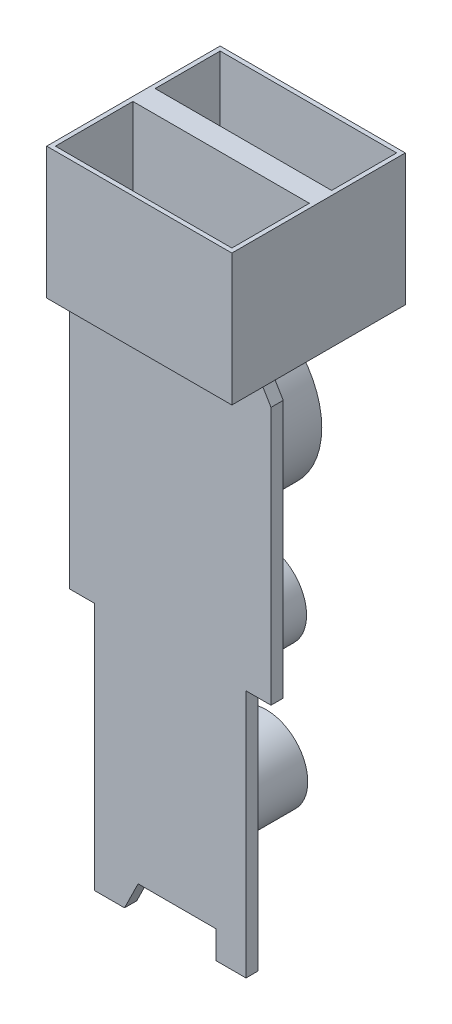
SolidWorks part; units mm, degrees
ref_plane "Front Plane" through (0, 0, 0) normal (0, 0, 1) x (1, 0, 0)
ref_plane "Top Plane" through (0, 0, 0) normal (0, 1, 0) x (1, 0, 0)
ref_plane "Right Plane" through (0, 0, 0) normal (1, 0, 0) x (0, 0, -1)
sketch "Sketch1" plane through (0, 0, 0) normal (0, 1, 0) x (1, 0, 0)
  line L10 (-7.035, 6.59) -> (7.035, 6.59)
  line L11 (-7.035, 6.59) -> (-7.035, -6.59)
  line L12 (-7.035, -6.59) -> (7.035, -6.59)
  line L13 (7.035, 6.59) -> (7.035, -6.59)
  point P0 (0, 0)
  point P5 (0, 0)
  point P6 (0, 0)
  dimension "D1" = 13.18
  dimension "D2" = 14.07
extrude "Boss-Extrude1" add sketch "Sketch1" along normal mid plane 10
sketch "Sketch2" plane through (0, 5, 0) normal (0, 1, 0) x (1, 0, 0)
  line L0 (7.035, 6.59) -> (-7.035, 6.59) construction
  line L1 (-6.705, 6.26) -> (6.705, 6.26)
  line L2 (-6.705, 6.26) -> (-6.705, 1.32)
  line L3 (-6.705, 1.32) -> (6.705, 1.32)
  line L4 (6.705, 6.26) -> (6.705, 1.32)
  line L5 (-7.035, 6.59) -> (-7.035, -6.59) construction
  line L6 (7.035, -6.59) -> (7.035, 6.59) construction
  line L11 (-7.035, -6.59) -> (7.035, -6.59) construction
  line L12 (-6.705, -0.3713) -> (6.705, -0.3713)
  line L13 (-6.705, -0.3713) -> (-6.705, -6.26)
  line L14 (-6.705, -6.26) -> (6.705, -6.26)
  line L15 (6.705, -0.3713) -> (6.705, -6.26)
  dimension "D1" = 0.33
  dimension "D2" = 0.33
  dimension "D3" = 0.33
  dimension "D4" = 0.33
  dimension "D5" = 1.6913
  dimension "D6" = 4.94
extrude "Cut-Extrude1" cut sketch "Sketch2" against normal blind 9
sketch "Sketch3" plane through (0, 0, 0) normal (0, 0, 1) x (1, 0, 0)
  line L0 (7.035, -5) -> (7.65, -6.0304)
  line L1 (7.65, -6.0304) -> (7.65, -25.6304)
  line L2 (7.65, -25.6304) -> (5.75, -25.6304)
  line L3 (5.75, -25.6304) -> (5.75, -44.5304)
  line L4 (5.75, -44.5304) -> (3.48, -44.5304)
  line L5 (3.48, -44.5304) -> (3.48, -42.4304)
  line L6 (3.48, -42.4304) -> (-2.449, -42.4304)
  line L9 (-7.035, -5) -> (7.035, -5)
  line L10 (-3.48, -44.5304) -> (-2.449, -42.4304)
  line L11 (-5.75, -44.5304) -> (-3.48, -44.5304)
  line L12 (-5.75, -25.6304) -> (-5.75, -44.5304)
  line L13 (-7.65, -25.6304) -> (-5.75, -25.6304)
  line L14 (-7.65, -6.0304) -> (-7.65, -25.6304)
  line L15 (-7.65, -6.0304) -> (-7.035, -5)
  dimension "D1" = 1.2
  dimension "D2" = 19.6
  dimension "D3" = 90
  dimension "D4" = 2.27
  dimension "D5" = 18.9
  dimension "D6" = 90
  dimension "D7" = 116.15
  dimension "D8" = 2.1
  dimension "D9" = 90
extrude "Boss-Extrude2" add sketch "Sketch3" along normal blind 0.93 from offset 3.3
sketch "Sketch5" plane through (0, 0, 0) normal (0, 0, 1) x (1, 0, 0)
  circle A0 centre (-1.283, -11.9672) radius 6.26
  circle A1 centre (-2.0272, -27.1608) radius 3.2
  circle A2 centre (-1.9521, -37.2217) radius 3.2
  dimension "D1" = 12.52
  dimension "D2" = 6.4
extrude "Boss-Extrude3" add sketch "Sketch5" against normal blind 5.6 from surface at 3.3 contours A0 starting at face at (0.0736, -27.6832, 3.3)
sketch "Sketch7" plane through (0, 0, 0) normal (0, 0, 1) x (1, 0, 0)
  circle A0 centre (-1.877, -27.386) radius 3.2
  dimension "D1" = 6.4
extrude "Boss-Extrude4" add sketch "Sketch7" against normal blind 8.1 from surface at 3.3 starting at face at (-7.543, -11.9672, 3.3)
sketch "Sketch8" plane through (0, 0, 0) normal (0, 0, 1) x (1, 0, 0)
  circle A0 centre (-1.9521, -38.4981) radius 3.165
  dimension "D1" = 6.33
extrude "Boss-Extrude5" add sketch "Sketch8" against normal blind 8.3 from surface at 3.3 starting at face at (-5.077, -27.386, 3.3)
